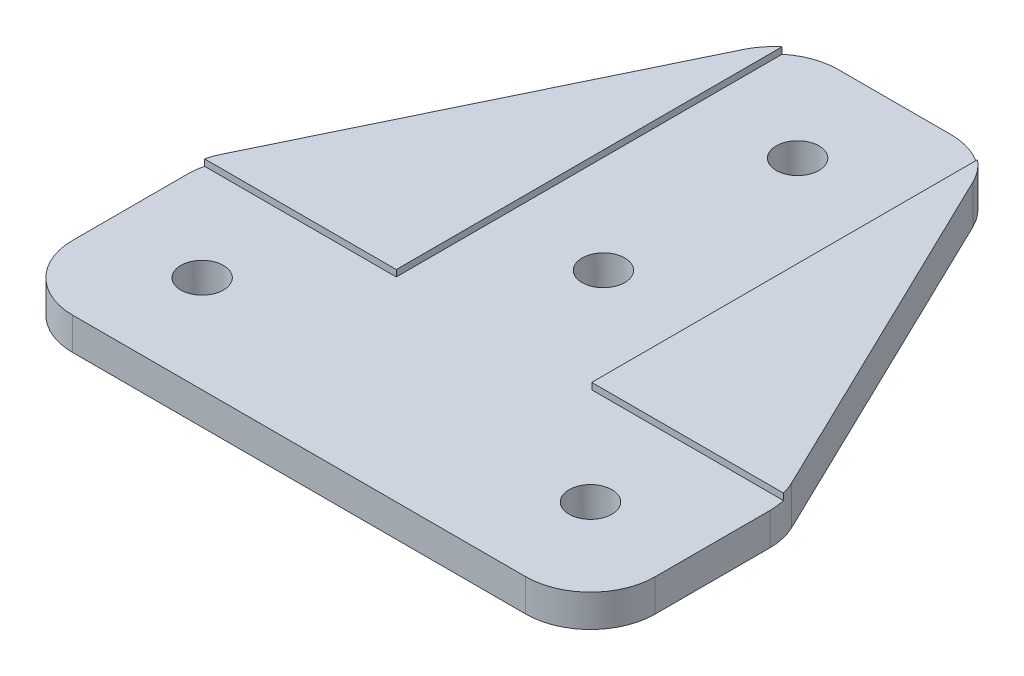
SolidWorks part; units mm, degrees
material "3.1325 (EN-AW 2017A)"
ref_plane "正面" through (0, 0, 0) normal (0, 0, 1) x (1, 0, 0)
ref_plane "平面" through (0, 0, 0) normal (0, 1, 0) x (1, 0, 0)
ref_plane "右側面" through (0, 0, 0) normal (1, 0, 0) x (0, 0, -1)
sketch "ｽｹｯﾁ1" plane through (0, 0, 0) normal (0, 1, 0) x (1, 0, 0)
  line L0 (0, 0) -> (45, 0)
  line L1 (45, 0) -> (45, 15)
  line L2 (45, 15) -> (30, 46)
  line L3 (30, 46) -> (15, 46)
  line L4 (15, 46) -> (0, 15)
  line L5 (0, 15) -> (0, 0)
  dimension "D1" = 15
  dimension "D2" = 45
  dimension "D3" = 31
  dimension "D4" = 15
  dimension "D5" = 15
  dimension "D6" = 15
extrude "ﾎﾞｽ - 押し出し1" add sketch "ｽｹｯﾁ1" along normal blind 3
sketch "ｽｹｯﾁ2" plane through (0, 3, 0) normal (0, 1, 0) x (1, 0, 0)
  line L0 (0, 15) -> (0, 0) construction
  line L1 (0, 0) -> (45, 0) construction
  line L2 (45, 0) -> (45, 15) construction
  line L3 (30, 46) -> (15, 46) construction
  circle A0 centre (7.5, 7.5) radius 1.65
  circle A1 centre (22.5, 38.5) radius 1.65
  circle A2 centre (22.5, 23.5) radius 1.65
  circle A3 centre (37.5, 7.5) radius 1.65
  dimension "D1" = 22.5
  dimension "D2" = 22.5
  dimension "D3" = 7.5
  dimension "D4" = 7.5
  dimension "D5" = 7.5
  dimension "D7" = 3.3
  dimension "D8" = 3.3
  dimension "D9" = 3.3
  dimension "D10" = 3.3
  dimension "D11" = 7.5
  dimension "D6" = 7.5
  dimension "D13" = 15
extrude "ｶｯﾄ - 押し出し1" cut sketch "ｽｹｯﾁ2" against normal blind 3
fillet "ﾌｨﾚｯﾄ1" radius 5 6 edges at (30, 1.5, -46) (15, 1.5, -46) (45, 1.5, -15) (45, 1.5, 0) (0, 1.5, -15) (0, 1.5, 0)
sketch "ｽｹｯﾁ3" plane through (0, 3, 0) normal (0, 1, 0) x (1, 0, 0)
  line L0 (0, 0) -> (45, 0)
  line L1 (0, 0) -> (0, 15.05)
  line L2 (45, 0) -> (45, 15.05)
  line L3 (0, 15.05) -> (14.95, 15.05)
  line L4 (5, 0) -> (40, 0) construction
  line L5 (14.95, 46) -> (30.05, 46)
  line L6 (14.95, 46) -> (14.95, 15.05)
  line L7 (30.05, 46) -> (30.05, 15.05)
  line L8 (14.95, 15.05) -> (30.05, 15.05) construction
  line L9 (26.8648, 46) -> (18.1352, 46) construction
  line L10 (0, 13.8539) -> (0, 5) construction
  line L11 (45, 5) -> (45, 13.8539) construction
  line L12 (30.05, 15.05) -> (45, 15.05)
  line L13 (14.95, 15.05) -> (30.05, 15.05) construction
  point P16 (22.5, 46)
  point P17 (22.5, 46)
  dimension "D1" = 15.1
  dimension "D2" = 15.05
extrude "ｶｯﾄ - 押し出し2" cut sketch "ｽｹｯﾁ3" against normal blind 0.5
